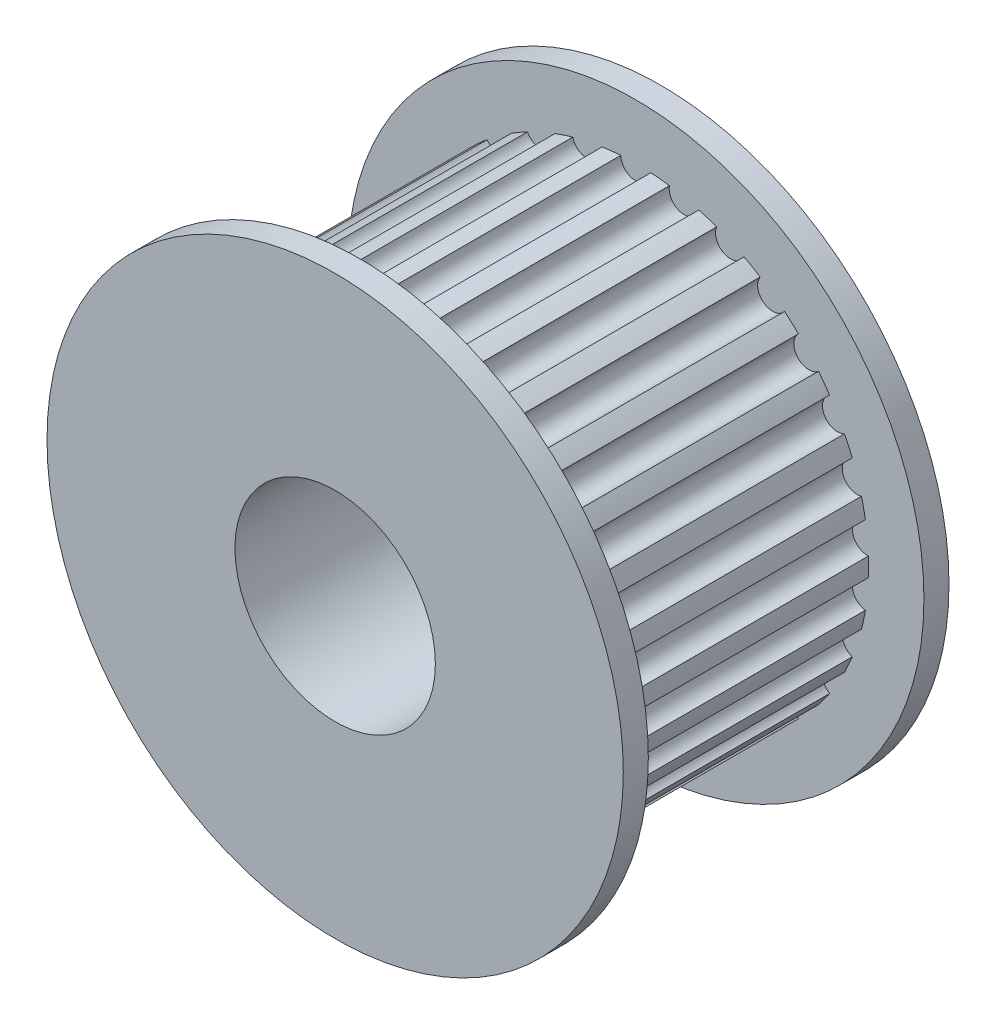
SolidWorks part; units mm, degrees
material "6061 合金"
ref_plane "前基準面" through (0, 0, 0) normal (0, 0, 1) x (1, 0, 0)
ref_plane "上基準面" through (0, 0, 0) normal (0, 1, 0) x (1, 0, 0)
ref_plane "右基準面" through (0, 0, 0) normal (1, 0, 0) x (0, 0, -1)
sketch "草圖1" plane through (0, 0, 0) normal (0, 0, 1) x (1, 0, 0)
  circle A0 centre (0, 0) radius 11.5
  dimension "D1" = 23
extrude "填料-伸長1" add sketch "草圖1" along normal mid plane 1
sketch "草圖2" plane through (0, 0, 0.5) normal (0, 0, 1) x (1, 0, 0)
  circle A0 centre (0, 0) radius 9.295
  dimension "D1" = 18.59
extrude "填料-伸長2" add sketch "草圖2" along normal blind 11
sketch "草圖7" plane through (0, 0, 11.5) normal (0, 0, 1) x (1, 0, 0)
  line L0 (0, 0) -> (0, 9.295) construction
  arc A0 (-0.5997, 9.2756) -> (0.5997, 9.2756) centre (0, 9.295) ccw
  circle A1 centre (0, 0) radius 9.295 construction
  circle A2 centre (0, 0) radius 9.295 construction
  arc A3 (-0.5997, 9.2756) -> (0.5997, 9.2756) centre (0, 0) cw
  point P10 (0, 8.695)
  dimension "D1" = 0.6
extrude "除料-伸長3" cut sketch "草圖7" against normal up to surface (11 mm away) up to face at (9.295, 0, 0.5)
sketch "草圖3" plane through (0, 0, 11.5) normal (0, 0, 1) x (1, 0, 0)
  circle A0 centre (0, 0) radius 11.5
  circle A1 centre (0, 0) radius 11.5 construction
extrude "填料-伸長3" add sketch "草圖3" along normal blind 1
sketch "草圖6" plane through (0, 0, -0.5) normal (0, 0, -1) x (-1, 0, 0)
  circle A0 centre (0, 0) radius 4
  dimension "D1" = 8
extrude "除料-伸長2" cut sketch "草圖6" against normal through all both and the other way through all
pattern_circular "環狀複製排列2" count 30 over 360 about axis through (0, 0, 0) along (0, 0, 1) of "除料-伸長3"
